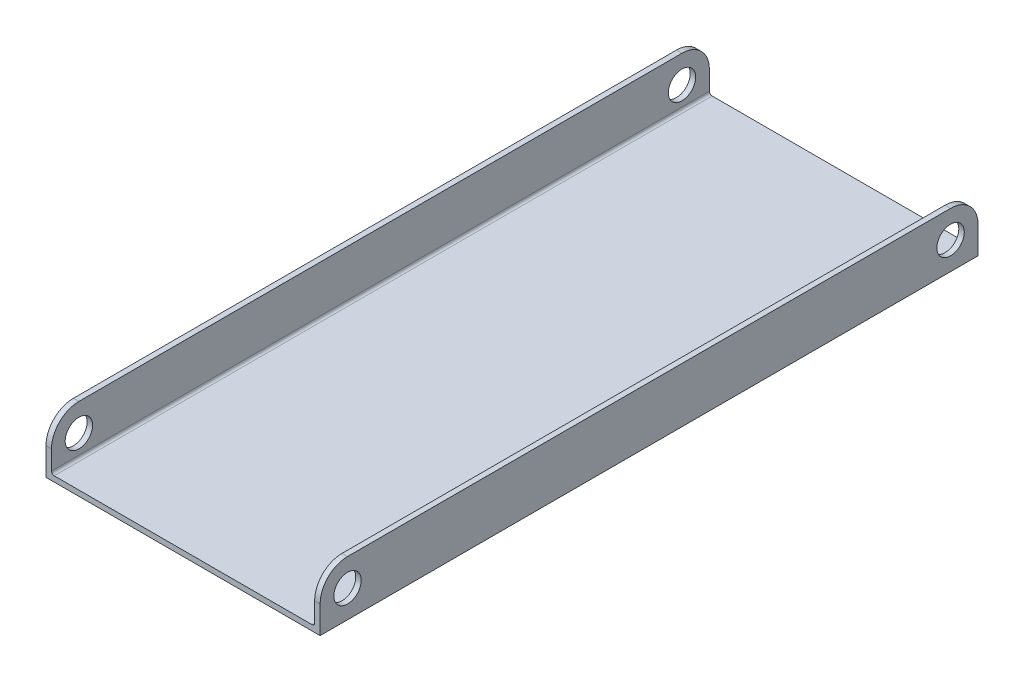
SolidWorks part; units mm, degrees
material "AISI 1020"
ref_plane "Front Plane" through (0, 0, 0) normal (0, 0, 1) x (1, 0, 0)
ref_plane "Top Plane" through (0, 0, 0) normal (0, 1, 0) x (1, 0, 0)
ref_plane "Right Plane" through (0, 0, 0) normal (1, 0, 0) x (0, 0, -1)
sketch "Sketch1" plane through (0, 0, 0) normal (0, 0, 1) x (1, 0, 0)
  line L0 (0, 0) -> (0, 16.9905) construction
  line L1 (-31.75, -6.35) -> (31.75, -6.35)
  line L2 (-31.75, -6.35) -> (-31.75, 6.35)
  line L3 (-31.75, 6.35) -> (31.75, 6.35)
  line L4 (31.75, -6.35) -> (31.75, 6.35)
  line L5 (-31.75, -6.35) -> (31.75, 6.35) construction
  line L6 (-31.75, 6.35) -> (31.75, -6.35) construction
  line L7 (-30.48, 6.35) -> (30.48, 6.35)
  line L8 (-30.48, 6.35) -> (-30.48, -5.08)
  line L9 (-30.48, -5.08) -> (30.48, -5.08)
  line L10 (30.48, 6.35) -> (30.48, -5.08)
  point P0 (0, 0)
  dimension "D1" = 63.5
  dimension "D2" = 60.96
  dimension "D3" = 1.27
  dimension "D4" = 12.7
extrude "Boss-Extrude1" add sketch "Sketch1" along normal blind 152.4 contours L3 L10 L9 L8 L2 L1 L4
sketch "Sketch2" plane through (31.75, 0, 0) normal (1, 0, 0) x (0, 0, -1)
  line L0 (-152.4, -6.35) -> (-152.4, 6.35) construction
  line L1 (-152.4, -6.35) -> (0, -6.35) construction
  line L2 (-76.2, 6.35) -> (-76.2, -27.9976) construction
  line L3 (-152.4, 6.35) -> (0, 6.35) construction
  circle A0 centre (-146.05, 0) radius 3.175
  circle A1 centre (-6.35, 0) radius 3.175
  dimension "D1" = 6.35
  dimension "D2" = 6.35
  dimension "D3" = 6.35
extrude "Cut-Extrude1" cut sketch "Sketch2" against normal through all
fillet "Fillet1" radius 6.35 4 edges at (-31.115, 6.35, 0) (31.115, 6.35, 0) (-31.115, 6.35, 152.4) (31.115, 6.35, 152.4)
fillet "Fillet2" radius 0.635 2 edges at (30.48, -5.08, 76.2) (-30.48, -5.08, 76.2)
